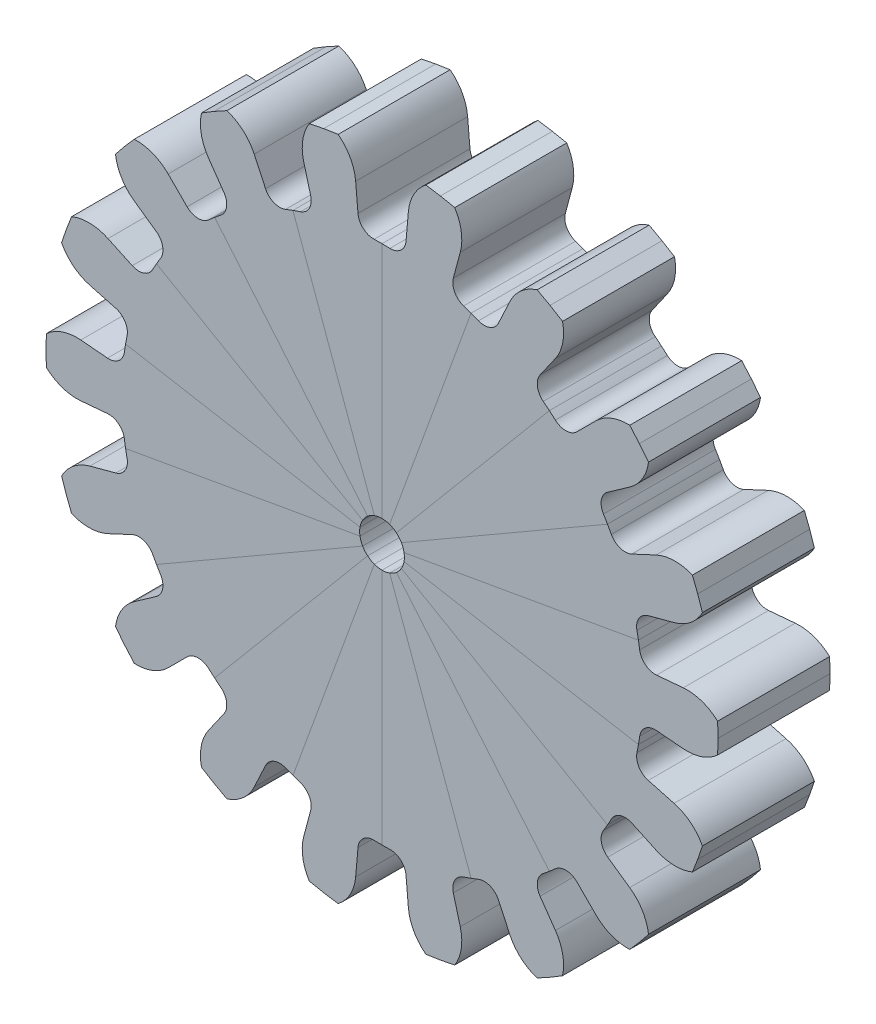
SolidWorks part; units mm, degrees
ref_plane "Plan de face" through (0, 0, 0) normal (0, 0, 1) x (1, 0, 0)
ref_plane "Plan de dessus" through (0, 0, 0) normal (0, 1, 0) x (1, 0, 0)
ref_plane "Plan de droite" through (0, 0, 0) normal (1, 0, 0) x (0, 0, -1)
sketch "Esquisse4" plane through (0, 0, 0) normal (0, 0, 1) x (1, 0, 0)
  line L0 (0, 0) -> (15.5601, 0) construction
  line L1 (0, 0) -> (17.2426, 1.5085) construction
  line L2 (0, 0) -> (17.0187, 3.0009) construction
  line L3 (0, 0) -> (17.2619, 0.7537) construction
  line L4 (11.5808, 1.0132) -> (13.4486, 1.1766)
  line L5 (11.4484, 2.0187) -> (0, 0)
  line L6 (14.9857, 0.6543) -> (15, 0)
  line L7 (14.9857, -0.6543) -> (15, 0)
  line L8 (11.5808, -1.0132) -> (13.4486, -1.1766)
  line L9 (11.4484, -2.0187) -> (0, 0)
  circle A0 centre (0, 0) radius 11.625 construction
  circle A1 centre (0, 0) radius 13.5 construction
  circle A2 centre (0, 0) radius 15 construction
  arc A3 (14.9857, 0.6543) -> (13.4486, 1.1766) centre (13.6242, -0.8297) ccw
  arc A4 (11.5808, 1.0132) -> (11.4484, 2.0187) centre (0, 0) ccw
  arc A5 (14.9857, -0.6543) -> (13.4486, -1.1766) centre (13.6242, 0.8297) cw
  arc A6 (11.5808, -1.0132) -> (11.4484, -2.0187) centre (0, 0) cw
  dimension "D1" = 30
  dimension "D2" = 27
  dimension "D3" = 23.25
  dimension "D4" = 10
  dimension "D5" = 5
  dimension "D6" = 2.5
extrude "Boss.-Extru.4" add sketch "Esquisse4" along normal blind 5 contours A6 L8 A5 L7 L6 A3 L4 A4 L5 L9
fillet "Congé1" radius 0.7 2 edges at (11.5808, 1.0132, 2.5) (11.5808, -1.0132, 2.5)
pattern_circular "Répétition circulaire1" count 18 over 360 about axis through (0, 0, 0) along (0, 0, 1) of bodies 103
sketch "Esquisse5" plane through (0, 0, 0) normal (0, 0, -1) x (-1, 0, 0)
  circle A0 centre (0, 0) radius 2.5
  dimension "D1" = 5
extrude "Enlèv. mat.-Extru.1" cut sketch "Esquisse5" against normal blind 3
sketch "Esquisse6" plane through (0, 0, 5) normal (0, 0, 1) x (1, 0, 0)
  circle A0 centre (0, 0) radius 1
  dimension "D1" = 2
extrude "Enlèv. mat.-Extru.2" cut sketch "Esquisse6" against normal blind 2
